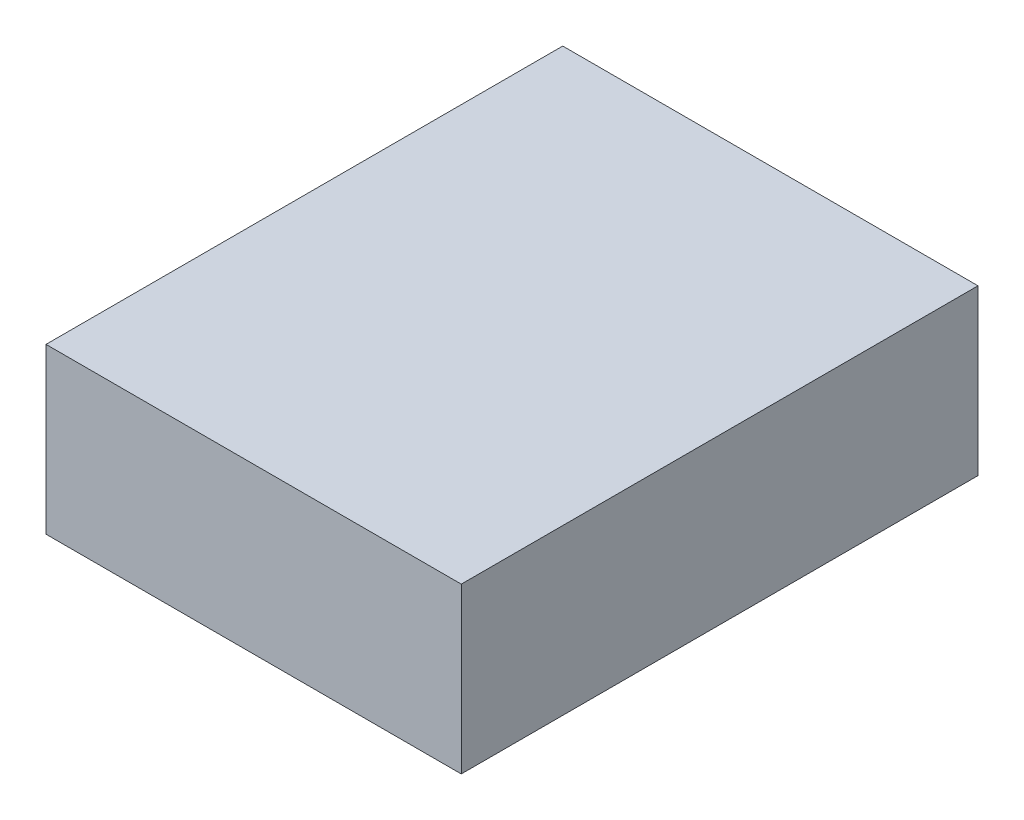
SolidWorks part; units mm, degrees
ref_plane "Спереди" through (0, 0, 0) normal (0, 0, 1) x (1, 0, 0)
ref_plane "Сверху" through (0, 0, 0) normal (0, 1, 0) x (1, 0, 0)
ref_plane "Справа" through (0, 0, 0) normal (1, 0, 0) x (0, 0, -1)
sketch "Эскиз1" plane through (0, 0, 0) normal (0, 1, 0) x (1, 0, 0)
  line L1 (0, 0) -> (442, 0)
  line L2 (0, 0) -> (0, 550)
  line L3 (0, 550) -> (442, 550)
  line L4 (442, 0) -> (442, 550)
  dimension "D1" = 442
  dimension "D2" = 550
extrude "Бобышка-Вытянуть1" add sketch "Эскиз1" along normal blind 175
